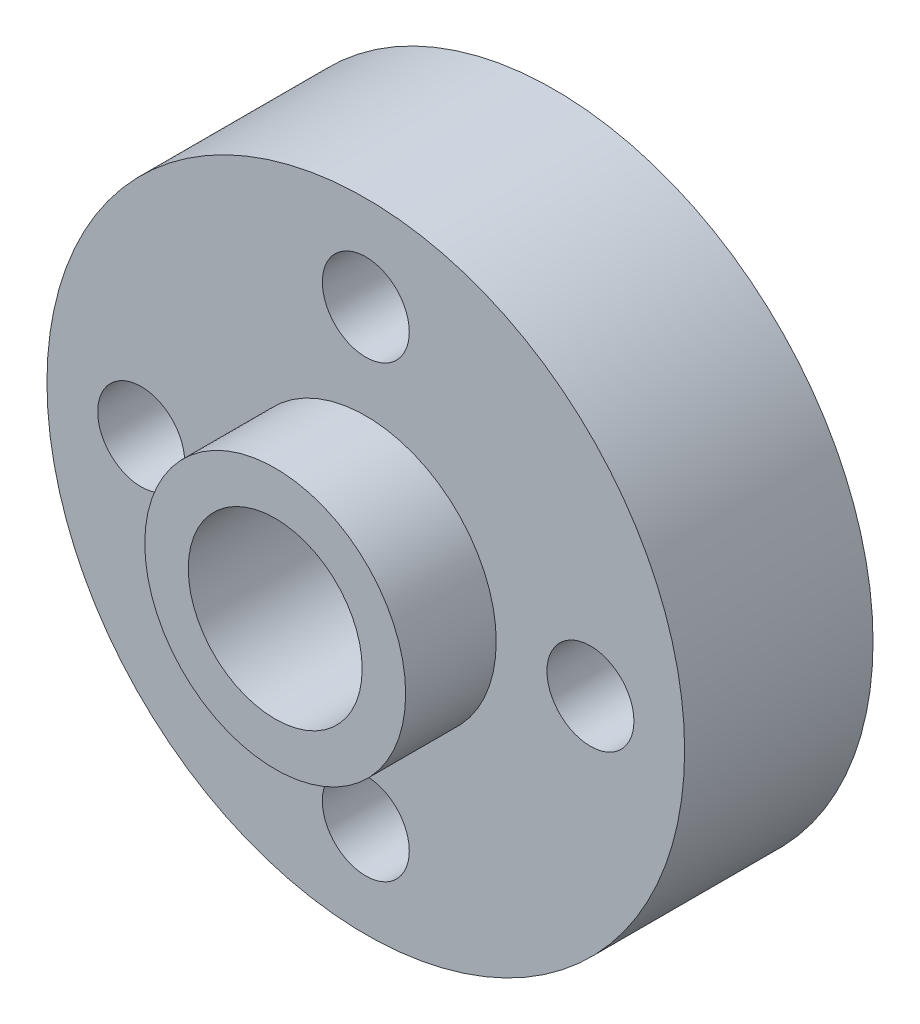
SolidWorks part; units mm, degrees
ref_plane "Plan de face" through (0, 0, 0) normal (0, 0, 1) x (1, 0, 0)
ref_plane "Plan de dessus" through (0, 0, 0) normal (0, 1, 0) x (1, 0, 0)
ref_plane "Plan de droite" through (0, 0, 0) normal (1, 0, 0) x (0, 0, -1)
sketch "Esquisse1" plane through (0, 0, 0) normal (0, 0, 1) x (1, 0, 0)
  circle A0 centre (0, 0) radius 11
  circle A1 centre (0, 0) radius 3
  dimension "D1" = 22
  dimension "D2" = 6
extrude "Extrusion1" add sketch "Esquisse1" along normal blind 6.5
sketch "Esquisse3" plane through (0, 0, 6.5) normal (0, 0, 1) x (1, 0, 0)
  circle A0 centre (0, 0) radius 3
  circle A1 centre (0, 0) radius 4.5
  dimension "D1" = 1.5
  dimension "D2" = 6
extrude "Extrusion2" add sketch "Esquisse3" along normal blind 3.125
sketch "Esquisse4" plane through (0, 0, 0) normal (0, 0, -1) x (-1, 0, 0)
  circle A0 centre (0, 0) radius 3
  circle A1 centre (0, 0) radius 4.5
  dimension "D1" = 6
  dimension "D2" = 1.5
extrude "Extrusion3" add sketch "Esquisse4" along normal blind 3.125
sketch "Esquisse5" plane through (0, 0, 6.5) normal (0, 0, 1) x (1, 0, 0)
  line L0 (0, 11) -> (0, -11) construction
  line L2 (11, 0) -> (-11, 0) construction
  line L3 (-11, 0) -> (-10.4274, 0) construction
  circle A0 centre (0, 0) radius 11 construction
  circle A1 centre (0, 7.75) radius 1.5
  circle A3 centre (0, -7.75) radius 1.5
  circle A4 centre (-7.75, 0) radius 1.5
  circle A5 centre (7.75, 0) radius 1.5
  dimension "D1" = 3
  dimension "D2" = 7.75
  dimension "D3" = 3
  dimension "D4" = 7.75
extrude "Enlèv. mat.-Extru.1" cut sketch "Esquisse5" against normal up to next
